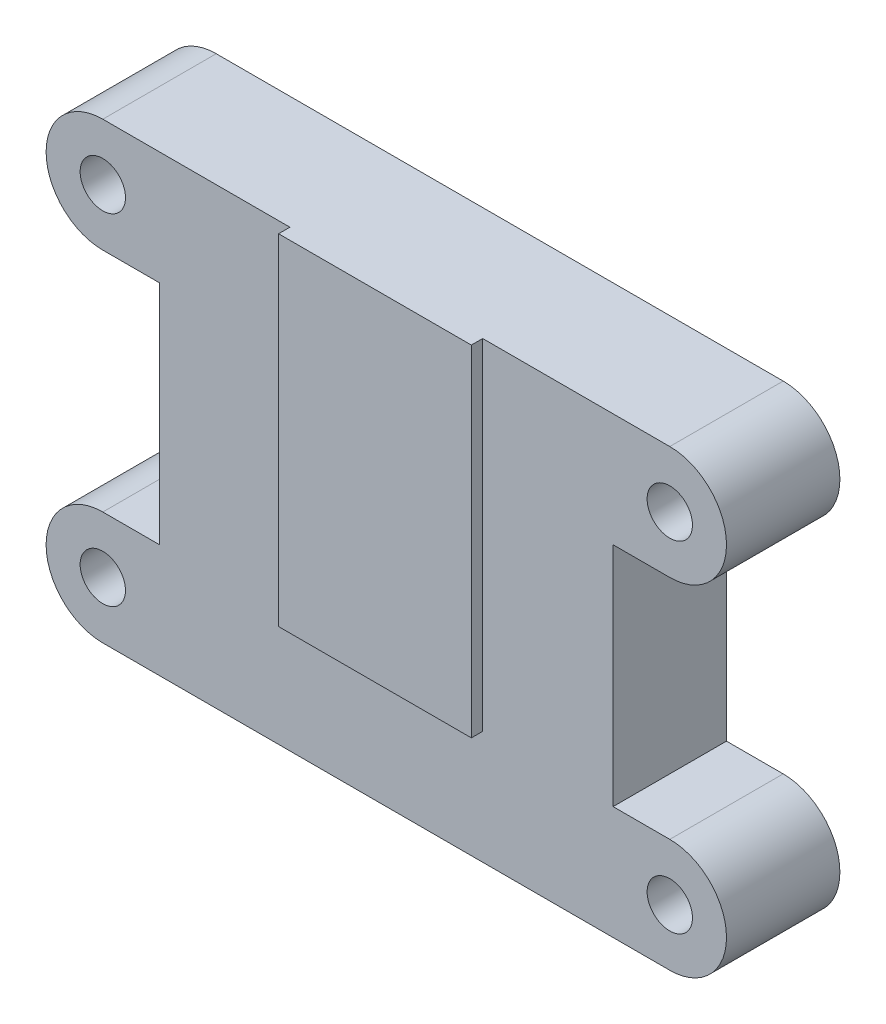
SolidWorks part; units mm, degrees
ref_plane "Front Plane" through (0, 0, 0) normal (0, 0, 1) x (1, 0, 0)
ref_plane "Top Plane" through (0, 0, 0) normal (0, 1, 0) x (1, 0, 0)
ref_plane "Right Plane" through (0, 0, 0) normal (1, 0, 0) x (0, 0, -1)
sketch "Sketch1" plane through (0, 0, 0) normal (0, 0, 1) x (1, 0, 0)
  line L0 (0, 0) -> (0, -50.8) construction
  line L1 (-31.75, 0) -> (31.75, 0)
  line L2 (31.75, -12.7) -> (25.4, -12.7)
  line L3 (-31.75, -12.7) -> (-25.4, -12.7)
  line L4 (25.4, -12.7) -> (25.4, -38.1)
  line L5 (-25.4, -12.7) -> (-25.4, -38.1)
  line L6 (25.4, -38.1) -> (31.75, -38.1)
  line L7 (-25.4, -38.1) -> (-31.75, -38.1)
  line L8 (31.75, -50.8) -> (0, -50.8)
  line L9 (-31.75, -50.8) -> (0, -50.8)
  arc A0 (31.75, 0) -> (31.75, -12.7) centre (31.75, -6.35) cw
  arc A1 (-31.75, 0) -> (-31.75, -12.7) centre (-31.75, -6.35) ccw
  arc A2 (31.75, -38.1) -> (31.75, -50.8) centre (31.75, -44.45) cw
  arc A3 (-31.75, -38.1) -> (-31.75, -50.8) centre (-31.75, -44.45) ccw
  circle A4 centre (-31.75, -6.35) radius 2.54
  circle A5 centre (31.75, -6.35) radius 2.54
  circle A6 centre (-31.75, -44.45) radius 2.54
  circle A7 centre (31.75, -44.45) radius 2.54
  dimension "D2" = 76.2
  dimension "D3" = 12.7
  dimension "D4" = 6.35
  dimension "D5" = 12.7
  dimension "D6" = 5.08
  dimension "D1" = 50.8
extrude "Boss-Extrude1" add sketch "Sketch1" along normal blind 12.7
sketch "Sketch2" plane through (0, 0, 12.7) normal (0, 0, 1) x (1, 0, 0)
  line L0 (31.75, 0) -> (-31.75, 0) construction
  line L1 (-10.795, 0) -> (10.795, 0)
  line L2 (-10.795, 0) -> (-10.795, -38.1)
  line L3 (-10.795, -38.1) -> (10.795, -38.1)
  line L4 (10.795, 0) -> (10.795, -38.1)
  line L5 (10.795, -38.1) -> (25.4, -38.1) construction
  line L6 (-10.795, -38.1) -> (-25.4, -38.1) construction
  dimension "D1" = 21.59
extrude "Boss-Extrude2" add sketch "Sketch2" along normal blind 1.27
